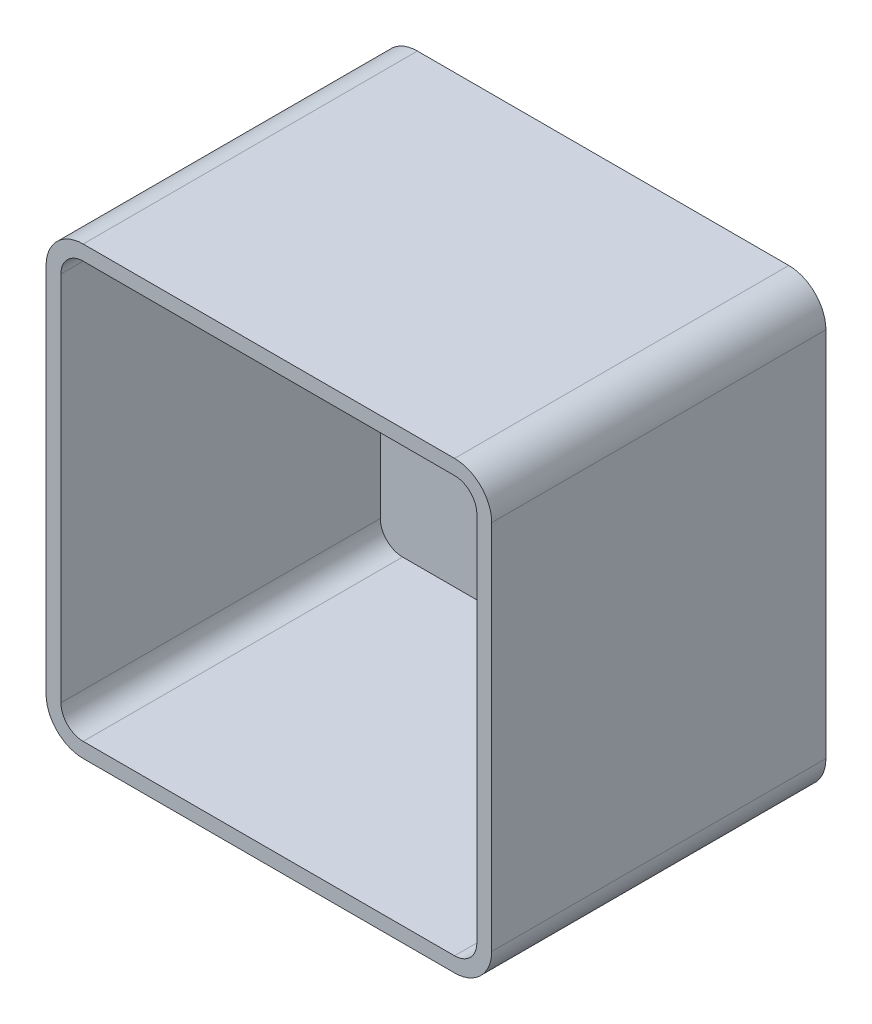
SolidWorks part; units mm, degrees
ref_plane "Front Plane" through (0, 0, 0) normal (0, 0, 1) x (1, 0, 0)
ref_plane "Top Plane" through (0, 0, 0) normal (0, 1, 0) x (1, 0, 0)
ref_plane "Right Plane" through (0, 0, 0) normal (1, 0, 0) x (0, 0, -1)
sketch "Sketch2" plane through (0, 0, 0) normal (0, 0, 1) x (1, 0, 0)
  line L1 (0, 0) -> (120, 0)
  line L2 (0, 0) -> (0, 120)
  line L3 (0, 120) -> (120, 120)
  line L4 (120, 0) -> (120, 120)
  dimension "D1" = 120
  dimension "D2" = 120
extrude "Boss-Extrude1" add sketch "Sketch2" along normal blind 90
fillet "Fillet1" radius 10 4 edges at (120, 0, 45) (0, 0, 45) (120, 120, 45) (0, 120, 45)
shell "Shell2" thickness 4
